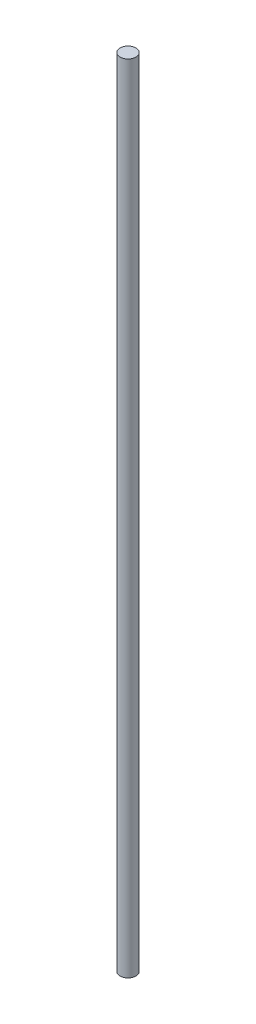
SolidWorks part; units mm, degrees
ref_plane "Alzado" through (0, 0, 0) normal (0, 0, 1) x (1, 0, 0)
ref_plane "Planta" through (0, 0, 0) normal (0, 1, 0) x (1, 0, 0)
ref_plane "Vista lateral" through (0, 0, 0) normal (1, 0, 0) x (0, 0, -1)
sketch "Croquis1" plane through (0, 0, 0) normal (0, 1, 0) x (1, 0, 0)
  circle A0 centre (0, 0) radius 4
  dimension "D1" = 8
extrude "Saliente-Extruir1" add sketch "Croquis1" along normal blind 400
